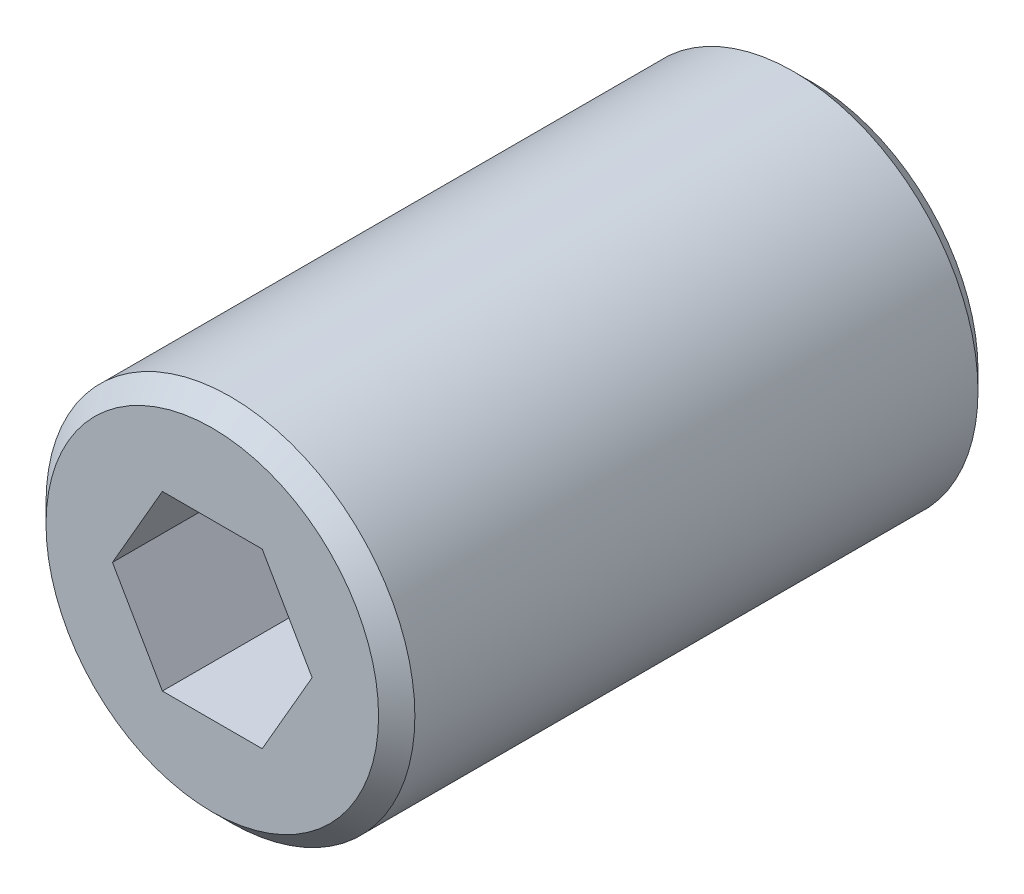
SolidWorks part; units mm, degrees
ref_plane "Front Plane" through (0, 0, 0) normal (0, 0, 1) x (1, 0, 0)
ref_plane "Top Plane" through (0, 0, 0) normal (0, 1, 0) x (1, 0, 0)
ref_plane "Right Plane" through (0, 0, 0) normal (1, 0, 0) x (0, 0, -1)
sketch "Sketch1" plane through (0, 0, 0) normal (0, 0, 1) x (1, 0, 0)
  line L1 (5.4993, 0) -> (2.7496, 4.7625)
  line L2 (2.7496, 4.7625) -> (-2.7496, 4.7625)
  line L3 (-2.7496, 4.7625) -> (-5.4993, 0)
  line L4 (-5.4993, 0) -> (-2.7496, -4.7625)
  line L5 (-2.7496, -4.7625) -> (2.7496, -4.7625)
  line L6 (2.7496, -4.7625) -> (5.4993, 0)
  circle A0 centre (0, 0) radius 10.16
  circle A1 centre (0, 0) radius 4.7625 construction
  dimension "D1" = 20.32
extrude "Boss-Extrude1" add sketch "Sketch1" along normal blind 33.02
chamfer "Chamfer1" distance 1 angle 45 2 edges at (10.16, 0, 0) (10.16, 0, 33.02)
